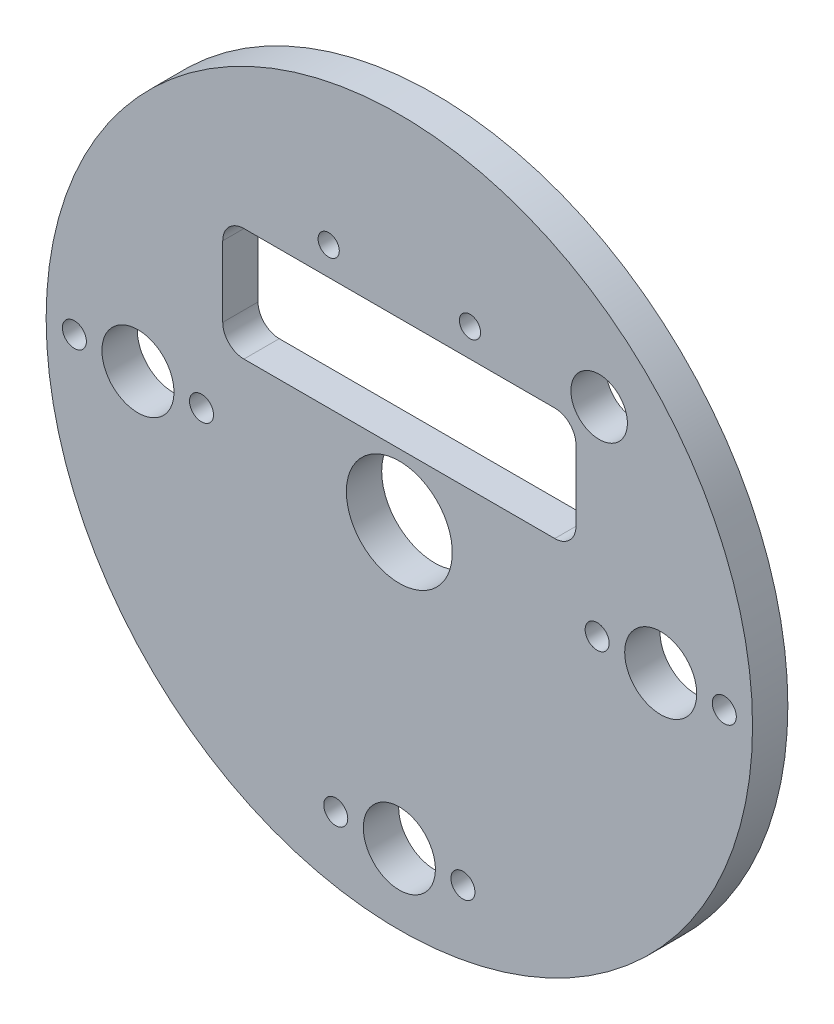
SolidWorks part; units mm, degrees
material "Acrylic (Medium-high impact)"
ref_plane "Front Plane" through (0, 0, 0) normal (0, 0, 1) x (1, 0, 0)
ref_plane "Top Plane" through (0, 0, 0) normal (0, 1, 0) x (1, 0, 0)
ref_plane "Right Plane" through (0, 0, 0) normal (1, 0, 0) x (0, 0, -1)
sketch "Sketch1" plane through (0, 0, 0) normal (0, 0, 1) x (1, 0, 0)
  circle A0 centre (0, 0) radius 50
  dimension "D1" = 100
extrude "Boss-Extrude1" add sketch "Sketch1" along normal blind 5
hole_wizard "Ø15.0 (15) Diameter Hole1" positions "Sketch3" profile "Sketch4" hole size "Ø15.0" standard "ISO" end condition through all
sketch "Sketch3" plane through (0, 0, 0) normal (0, 0, -1) x (-1, 0, 0)
  point P0 (0, 0)
sketch "Sketch4" plane through (0, 0, 0) normal (1, 0, 0) x (0, 1, 0)
  line L0 (0, 0) -> (0, 5)
  line L1 (0, 5) -> (7.5, 5)
  line L2 (7.5, 5) -> (7.5, 0)
  line L5 (7.5, 0) -> (0, 0)
  line L11 (0, -6.35) -> (0, 107.95) construction
  dimension "Thru Hole Dia." = 15
  dimension "Thru Hole Depth" = 5
hole_wizard "Ø10.2 (10.2) Diameter Hole1" positions "Sketch5" profile "Sketch6" hole size "Ø10.2" standard "ISO"
sketch "Sketch5" plane through (0, 0, 0) normal (0, 0, -1) x (-1, 0, 0)
  point P4 (37, 0)
  point P17 (-37, 0)
  point P18 (0, 0)
  point P21 (0, -37)
  point P23 (0, -40)
  dimension "D1" = 3
  dimension "D2" = 40
  dimension "D3" = 37
sketch "Sketch6" plane through (-37, 0, 0) normal (1, 0, 0) x (0, 1, 0)
  line L0 (0, 0) -> (0, 5)
  line L1 (0, 5) -> (5.1, 5)
  line L2 (5.1, 5) -> (5.1, 0)
  line L5 (5.1, 0) -> (0, 0)
  line L11 (0, -6.35) -> (0, 107.95) construction
  dimension "Thru Hole Dia." = 10.2
  dimension "Thru Hole Depth" = 5
hole_wizard "M3 Clearance Hole1" positions "Sketch7" profile "Sketch8" hole size "M3" standard "ISO" end condition through all
sketch "Sketch7" plane through (0, 0, 5) normal (0, 0, 1) x (1, 0, 0)
  circle A0 centre (37, 0) radius 5.1 construction
  circle A1 centre (0, -40) radius 5.1 construction
  point P0 (46, 0)
  point P2 (28, 0)
  point P11 (9, -40)
  point P13 (-9, -40)
  point P46 (-46, 0)
  point P47 (-28, 0)
  dimension "D2" = 9
  dimension "D1" = 9
  dimension "D4" = 9
  dimension "D5" = 9
  dimension "D6" = 2
  dimension "D3" = 40
sketch "Sketch8" plane through (46, 0, 5) normal (1, 0, 0) x (0, -1, 0)
  line L0 (0, 0) -> (0, 5)
  line L1 (0, 5) -> (1.7, 5)
  line L2 (1.7, 5) -> (1.7, 0)
  line L5 (1.7, 0) -> (0, 0)
  line L11 (0, -6.35) -> (0, 107.95) construction
  dimension "Thru Hole Dia." = 3.4
  dimension "Thru Hole Depth" = 5
sketch "Sketch9" plane through (0, 0, 5) normal (0, 0, 1) x (1, 0, 0)
  line L1 (-22, 25) -> (22, 25)
  line L2 (-25, 22) -> (-25, 12)
  line L3 (-22, 9) -> (22, 9)
  line L4 (25, 22) -> (25, 12)
  line L5 (-25, 25) -> (25, 9) construction
  line L6 (-25, 9) -> (25, 25) construction
  arc A0 (-25, 12) -> (-22, 9) centre (-22, 12) ccw
  arc A1 (25, 12) -> (22, 9) centre (22, 12) cw
  arc A2 (25, 22) -> (22, 25) centre (22, 22) ccw
  arc A3 (-25, 22) -> (-22, 25) centre (-22, 22) cw
  point P0 (0, 17)
  dimension "D4" = 3
  dimension "D1" = 17
  dimension "D2" = 16
  dimension "D3" = 50
extrude "Cut-Extrude1" cut sketch "Sketch9" against normal blind 10
sketch "Sketch10" plane through (0, 0, 5) normal (0, 0, 1) x (1, 0, 0)
  line L0 (-25, 22) -> (-25, 12) construction
  line L1 (25, 12) -> (25, 22) construction
  line L3 (-22, 9) -> (22, 9) construction
  circle A0 centre (-10, 29) radius 1.5
  circle A1 centre (10, 29) radius 1.5
  dimension "D1" = 3
  dimension "D2" = 3
  dimension "D3" = 15
  dimension "D4" = 15
  dimension "D5" = 20
extrude "Cut-Extrude2" cut sketch "Sketch10" against normal blind 10
sketch "Sketch11" plane through (0, 0, 5) normal (0, 0, 1) x (1, 0, 0)
  line L0 (0, 0) -> (28.2843, 28.2843) construction
  line L1 (0, 0) -> (19.6203, 0) construction
  circle A0 centre (28.2843, 28.2843) radius 4
  dimension "D1" = 8
  dimension "D2" = 45
  dimension "D3" = 40
extrude "Cut-Extrude3" cut sketch "Sketch11" against normal blind 10
